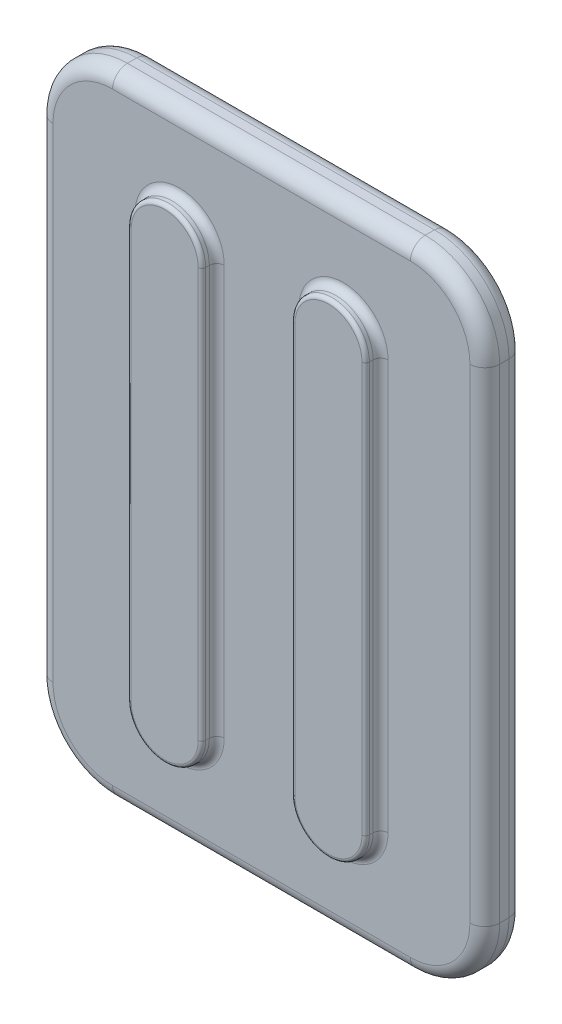
SolidWorks part; units mm, degrees
ref_plane "前视基准面" through (0, 0, 0) normal (0, 0, 1) x (1, 0, 0)
ref_plane "上视基准面" through (0, 0, 0) normal (0, 1, 0) x (1, 0, 0)
ref_plane "右视基准面" through (0, 0, 0) normal (1, 0, 0) x (0, 0, -1)
sketch "草图1" plane through (0, 0, 0) normal (0, 0, 1) x (1, 0, 0)
  line L1 (-300, 425) -> (300, 425)
  line L2 (-300, 425) -> (-300, -425)
  line L3 (-300, -425) -> (300, -425)
  line L4 (300, 425) -> (300, -425)
  line L5 (-300, 425) -> (300, -425) construction
  line L6 (-300, -425) -> (300, 425) construction
  point P0 (0, 0)
  dimension "D1" = 600
  dimension "D2" = 850
extrude "凸台-拉伸1" add sketch "草图1" along normal blind 52.4849
sketch "草图2" plane through (0, 0, 52.4849) normal (0, 0, 1) x (1, 0, 0)
  line L0 (0, 425) -> (0, -425) construction
  line L1 (300, 425) -> (-300, 425) construction
  line L2 (-300, -425) -> (300, -425) construction
  line L3 (-110, 275) -> (-110, -275) construction
  line L4 (-60, 275) -> (-60, -275)
  line L5 (-160, 275) -> (-160, -275)
  line L6 (110, 275) -> (110, -275) construction
  line L7 (60, 275) -> (60, -275)
  line L8 (160, 275) -> (160, -275)
  arc A0 (-60, 275) -> (-160, 275) centre (-110, 275) ccw
  arc A1 (-160, -275) -> (-60, -275) centre (-110, -275) ccw
  arc A2 (60, 275) -> (160, 275) centre (110, 275) cw
  arc A3 (160, -275) -> (60, -275) centre (110, -275) cw
  point P8 (-110, 0)
  point P16 (110, 0)
  dimension "D2" = 50
  dimension "D1" = 550
  dimension "D3" = 110
extrude "凸台-拉伸2" add sketch "草图2" along normal blind 20
fillet "圆角1" radius 100 4 edges at (300, 425, 26.2425) (-300, 425, 26.2425) (300, -425, 26.2425) (-300, -425, 26.2425)
fillet "圆角2" radius 10 8 edges at (110, 325, 52.4849) (160, 0, 52.4849) (110, -325, 52.4849) (-110, 325, 52.4849) (-60, 0, 52.4849) (-110, -325, 52.4849) (60, 0, 52.4849) (-160, 0, 52.4849)
fillet "圆角3" radius 5 8 edges at (-60, 0, 72.4849) (-110, -325, 72.4849) (-160, 0, 72.4849) (-110, 325, 72.4849) (160, 0, 72.4849) (110, -325, 72.4849) (60, 0, 72.4849) (110, 325, 72.4849)
fillet "圆角4" radius 20 16 edges at (-270.7107, 395.7107, 0) (0, 425, 0) (270.7107, 395.7107, 0) (300, 0, 0) (270.7107, -395.7107, 0) (0, -425, 0) (-270.7107, -395.7107, 0) (-270.7107, 395.7107, 52.4849) (0, 425, 52.4849) (270.7107, 395.7107, 52.4849) (300, 0, 52.4849) (270.7107, -395.7107, 52.4849) (0, -425, 52.4849) (-270.7107, -395.7107, 52.4849) (-300, 0, 0) (-300, 0, 52.4849)
sketch "草图3" plane through (0, 425, 0) normal (0, 1, 0) x (1, 0, 0)
  line L0 (0, 0) -> (0, 122.9159) construction
  line L1 (-159.75, 0) -> (-110.25, 0)
  line L2 (-200, 0) -> (-280, 0) construction
  line L3 (200, 0) -> (-200, 0) construction
  line L4 (-110.25, 0) -> (-110.25, 7.38)
  line L5 (-110.25, 7.38) -> (-122.225, 19.39)
  line L6 (-122.225, 19.39) -> (-147.775, 19.39)
  line L7 (-135, 0) -> (-135, 19.39) construction
  line L8 (-159.75, 7.38) -> (-147.775, 19.39)
  line L9 (-159.75, 0) -> (-159.75, 7.38)
  line L10 (135, 0) -> (135, 19.39) construction
  line L11 (159.75, 0) -> (159.75, 7.38)
  line L12 (159.75, 7.38) -> (147.775, 19.39)
  line L13 (122.225, 19.39) -> (147.775, 19.39)
  line L14 (110.25, 7.38) -> (122.225, 19.39)
  line L15 (110.25, 0) -> (110.25, 7.38)
  line L16 (159.75, 0) -> (110.25, 0)
  dimension "D1" = 49.5
  dimension "D2" = 25.55
  dimension "D3" = 7.38
  dimension "D4" = 19.39
  dimension "D5" = 220.5
extrude "凸台-拉伸3" add sketch "草图3" against normal blind 670 from offset 100 offset against normal yes
